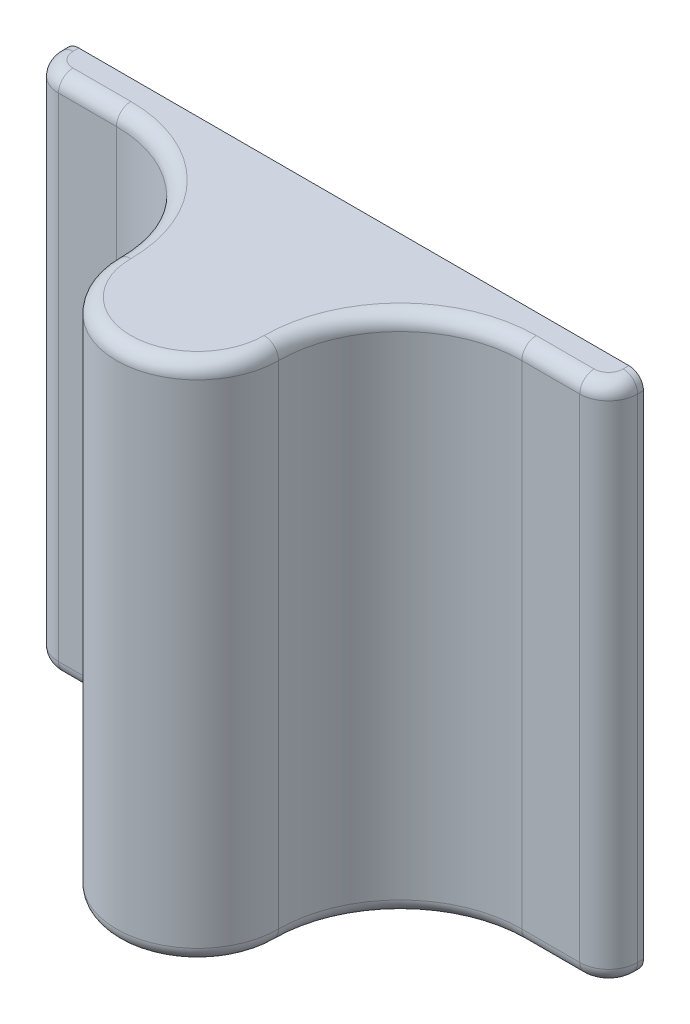
SolidWorks part; units mm, degrees
ref_plane "Спереди" through (0, 0, 0) normal (0, 0, 1) x (1, 0, 0)
ref_plane "Сверху" through (0, 0, 0) normal (0, 1, 0) x (1, 0, 0)
ref_plane "Справа" through (0, 0, 0) normal (1, 0, 0) x (0, 0, -1)
ref_plane "Plane1" through (0, 0, 0) normal (0, -1, 0) x (-1, 0, 0)
sketch "Sketch3" plane through (0, 0, 0) normal (0, -1, 0) x (-1, 0, 0)
  line L0 (-12.6693, -22) -> (-12.6693, -12.9031) construction
  line L1 (-10.6693, -22) -> (-14.6693, -22) construction
  line L2 (-10.6693, -12) -> (-10.6693, -22) construction
  line L3 (42.1, -15.6) -> (-42.1, -15.6) construction
  line L4 (-12.6693, -16.6) -> (-2.6693, -16.6)
  line L5 (-2.6693, -16.6) -> (-2.6693, -16.8)
  line L6 (-3.6693, -17.8) -> (-5.6693, -17.8)
  line L9 (-9.8693, -14.3159) -> (-9.8693, -25.3827) construction
  line L10 (-21.6693, -17.8) -> (-19.6693, -17.8)
  line L11 (-22.6693, -16.6) -> (-22.6693, -16.8)
  line L12 (-12.6693, -16.6) -> (-22.6693, -16.6)
  arc A0 (-9.8693, -22) -> (-15.4693, -22) centre (-12.6693, -22) cw
  arc A1 (-5.6693, -17.8) -> (-9.8693, -22) centre (-5.6693, -22) ccw
  arc A2 (-2.6693, -16.8) -> (-3.6693, -17.8) centre (-3.6693, -16.8) cw
  arc A3 (-22.6693, -16.8) -> (-21.6693, -17.8) centre (-21.6693, -16.8) ccw
  arc A4 (-19.6693, -17.8) -> (-15.4693, -22) centre (-19.6693, -22) cw
  dimension "D1" = 0.8
  dimension "D6" = 1
  dimension "D7" = 10
  dimension "D2" = 1
  dimension "D5" = 1.2
extrude "Boss-Extrude2" add sketch "Sketch3" along normal mid plane 18
fillet "Fillet1" radius 0.5 18 edges at (22.6693, 9, 16.7) (22.3764, 9, 17.5071) (20.6693, 9, 17.8) (2.6693, 9, 16.7) (2.9622, 9, 17.5071) (4.6693, 9, 17.8) (8.6392, 9, 19.0302) (12.6693, 9, 24.8) (22.6693, -9, 16.7) (22.3764, -9, 17.5071) (20.6693, -9, 17.8) (2.6693, -9, 16.7) (2.9622, -9, 17.5071) (4.6693, -9, 17.8) (8.6392, -9, 19.0302) (12.6693, -9, 24.8) (16.6995, 9, 19.0302) (16.6995, -9, 19.0302)
sketch "Sketch4" plane through (0, 0, 16.6) normal (0, 0, -1) x (-1, 0, 0)
  line L0 (-14.8693, 0.8) -> (-14.8693, -0.8)
  line L1 (-14.6693, 0.6) -> (-10.6693, 0.6) construction
  line L2 (-14.6693, 0.6) -> (-14.6693, -0.6) construction
  line L3 (-14.6693, -0.6) -> (-10.6693, -0.6) construction
  line L4 (-10.6693, 0.6) -> (-10.6693, -0.6) construction
  line L5 (-14.8693, -0.8) -> (-14.7693, -0.8)
  line L6 (-10.4693, 0.8) -> (-10.4693, -0.8)
  line L7 (-14.8693, 0.8) -> (-14.7693, 0.8)
  line L8 (-12.6693, 0.65) -> (-12.6693, -0.65) construction
  line L9 (-13.9693, 0.8) -> (-11.3693, 0.8)
  line L10 (-14.8693, 0) -> (-10.4693, 0) construction
  line L11 (-14.8693, 0.8) -> (-10.4693, 0.8) construction
  line L12 (-10.5693, 0.8) -> (-10.4693, 0.8)
  line L13 (-10.5693, -0.8) -> (-10.4693, -0.8)
  line L14 (-13.9693, -0.8) -> (-11.3693, -0.8)
  line L15 (-14.8693, -0.8) -> (-10.4693, -0.8) construction
  arc A0 (-14.7693, 0.8) -> (-13.9693, 0.8) centre (-14.3693, 1.1) ccw
  arc A1 (-10.5693, 0.8) -> (-11.3693, 0.8) centre (-10.9693, 1.1) cw
  arc A2 (-10.5693, -0.8) -> (-11.3693, -0.8) centre (-10.9693, -1.1) ccw
  arc A3 (-14.7693, -0.8) -> (-13.9693, -0.8) centre (-14.3693, -1.1) cw
  point P26 (-12.6693, 0)
  dimension "D2" = 1
  dimension "D1" = 0.2
extrude "Cut-Extrude1" cut sketch "Sketch4" against normal up to surface (5.4 mm away)
